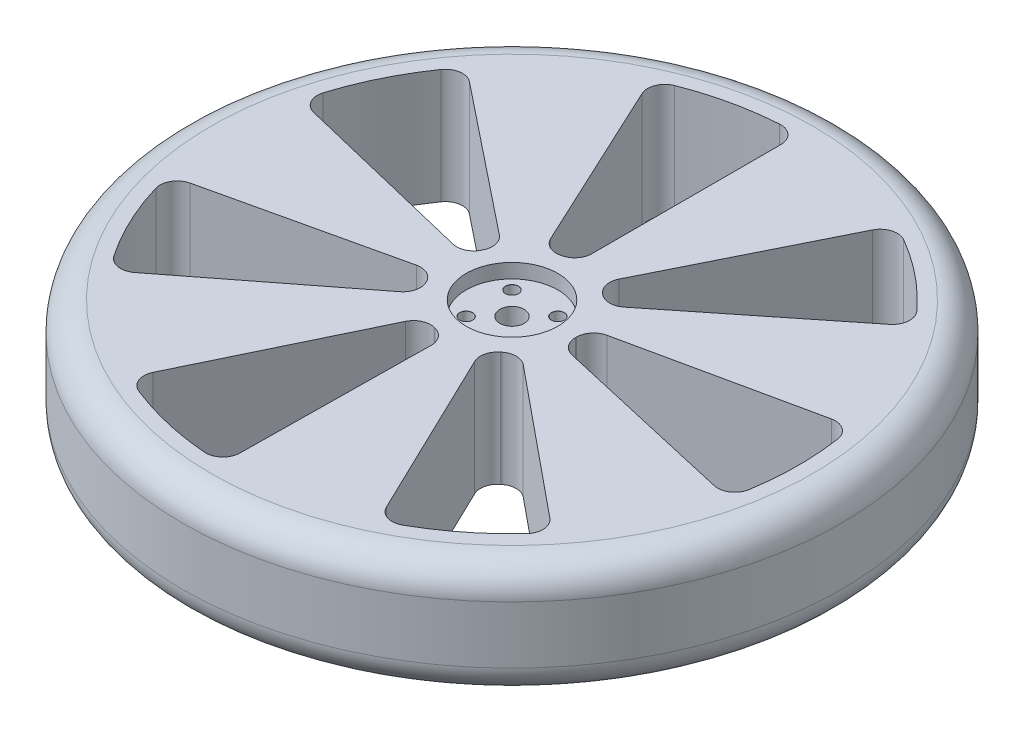
SolidWorks part; units mm, degrees
ref_plane "Front Plane" through (0, 0, 0) normal (0, 0, 1) x (1, 0, 0)
ref_plane "Top Plane" through (0, 0, 0) normal (0, 1, 0) x (1, 0, 0)
ref_plane "Right Plane" through (0, 0, 0) normal (1, 0, 0) x (0, 0, -1)
sketch "Sketch1" plane through (0, 0, 0) normal (0, 1, 0) x (1, 0, 0)
  circle A0 centre (0, 0) radius 115
  dimension "D1" = 230
extrude "Boss-Extrude1" add sketch "Sketch1" along normal blind 40
sketch "Sketch2" plane through (0, 40, 0) normal (0, 1, 0) x (1, 0, 0)
  line L0 (0, 0) -> (0, 100)
  line L1 (0, 0) -> (-42.2618, 90.6308)
  circle A2 centre (0, 0) radius 100
  circle A3 centre (0, 0) radius 22.5
  dimension "D1" = 45
  dimension "D3" = 200
  dimension "D2" = 25
extrude "Cut-Extrude1" cut sketch "Sketch2" against normal blind 40
fillet "Fillet1" radius 6 4 edges at (0, 20, -100) (-42.2618, 20, -90.6308) (0, 20, -22.5) (-9.5089, 20, -20.3919)
sketch "Sketch3" plane through (0, 40, 0) normal (0, 1, 0) x (1, 0, 0)
  circle A0 centre (0, 0) radius 4.25
  dimension "D1" = 8.5
extrude "Cut-Extrude2" cut sketch "Sketch3" against normal blind 40
pattern_circular "CirPattern1" count 7 over 360 about axis through (0, 0, 0) along (0, 1, 0) of "Fillet1", "Cut-Extrude1"
ref_plane "Plane1" through (0, 20, 0) normal (0, 1, 0) x (1, 0, 0)
sketch "Sketch4" plane through (0, 40, 0) normal (0, 1, 0) x (1, 0, 0)
  circle A0 centre (0, 0) radius 16
  dimension "D1" = 32
extrude "Cut-Extrude3" cut sketch "Sketch4" against normal blind 5
hole_wizard "M4 Clearance Hole1" positions "Sketch8" profile "Sketch6" hole size "M4" standard "ANSI Metric"
sketch "Sketch8" plane through (0, 35, 0) normal (0, 1, 0) x (1, 0, 0)
  point P0 (8, 8)
  point P2 (-8, 8)
  point P4 (-8, -8)
  point P6 (8, -8)
  dimension "D1" = 8
  dimension "D2" = 8
  dimension "D3" = 8
  dimension "D4" = 8
sketch "Sketch6" plane through (8, 35, -8) normal (1, 0, 0) x (0, 0, 1)
  line L0 (0, 0) -> (0, 14.3519)
  line L1 (0, 14.3519) -> (2.25, 13)
  line L2 (2.25, 13) -> (2.25, 0.025)
  line L3 (2.25, 0.025) -> (2.275, 0)
  line L5 (2.275, 0) -> (0, 0)
  line L6 (-2.25, 0.025) -> (-2.275, 0) construction
  line L10 (0, 14.3519) -> (-2.25, 13) construction
  line L11 (0, -6.35) -> (0, 107.95) construction
  dimension "Hole Dia." = 4.5
  dimension "Hole Depth" = 13
  dimension "Near C'Sink Dia." = 4.55
  dimension "Near C'Sink Angle" = 90
  dimension "Drill Angle" = 118
fillet "Fillet2" radius 10 2 edges at (0, 0, 115) (0, 40, 115)
